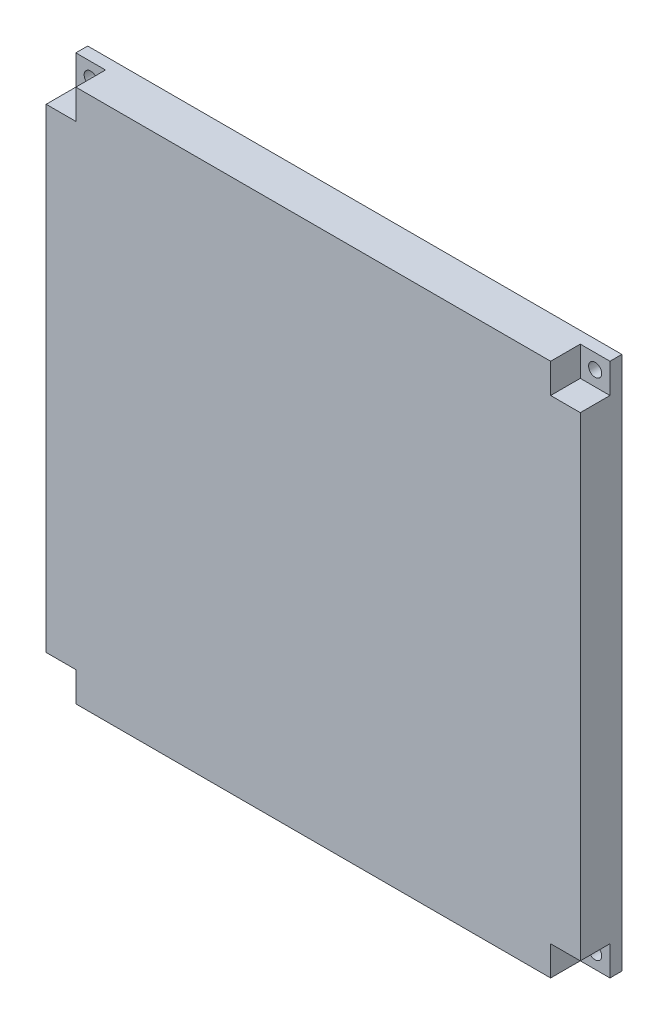
SolidWorks part; units mm, degrees
ref_plane "前基準面" through (0, 0, 0) normal (0, 0, 1) x (1, 0, 0)
ref_plane "上基準面" through (0, 0, 0) normal (0, 1, 0) x (1, 0, 0)
ref_plane "右基準面" through (0, 0, 0) normal (1, 0, 0) x (0, 0, -1)
sketch "草圖1" plane through (0, 0, 0) normal (0, 0, 1) x (1, 0, 0)
  line L1 (-89.0867, 42.9814) -> (10.9133, 42.9814)
  line L2 (-89.0867, 42.9814) -> (-89.0867, -47.0186)
  line L3 (-89.0867, -47.0186) -> (10.9133, -47.0186)
  line L4 (10.9133, 42.9814) -> (10.9133, -47.0186)
  dimension "D1" = 90
  dimension "D2" = 100
extrude "填料-伸長1" add sketch "草圖1" along normal blind 10 contours L4 L3 L2 L1
ref_plane "平面1" through (0, 0, 10) normal (0, 0, 1) x (1, 0, 0)
sketch "草圖6" plane through (0, 0, 10) normal (0, 0, 1) x (1, 0, 0)
  line L0 (-89.0867, -2.0186) -> (10.9133, -2.0186) construction
  line L1 (-89.0867, 42.9814) -> (-89.0867, -47.0186) construction
  line L2 (10.9133, 42.9814) -> (10.9133, -47.0186) construction
  line L3 (-39.0867, 42.9814) -> (-39.0867, -47.0186) construction
  line L4 (-89.0867, 42.9814) -> (10.9133, 42.9814) construction
  line L5 (-89.0867, -47.0186) -> (10.9133, -47.0186) construction
  line L6 (5.9133, 37.9814) -> (0.9133, 37.9814)
  line L7 (-84.0867, 42.9814) -> (-79.0867, 42.9814)
  line L8 (-84.0867, 42.9814) -> (-84.0867, 37.9814)
  line L9 (-84.0867, 37.9814) -> (-79.0867, 37.9814)
  line L10 (-79.0867, 42.9814) -> (-79.0867, 37.9814)
  line L11 (0.9133, 42.9814) -> (0.9133, 37.9814)
  line L12 (5.9133, 42.9814) -> (0.9133, 42.9814)
  line L13 (5.9133, 42.9814) -> (5.9133, 37.9814)
  line L14 (-84.0867, -42.0186) -> (-79.0867, -42.0186)
  line L15 (-79.0867, -47.0186) -> (-79.0867, -42.0186)
  line L16 (-84.0867, -47.0186) -> (-79.0867, -47.0186)
  line L17 (-84.0867, -47.0186) -> (-84.0867, -42.0186)
  line L18 (5.9133, -47.0186) -> (5.9133, -42.0186)
  line L19 (5.9133, -47.0186) -> (0.9133, -47.0186)
  line L20 (0.9133, -47.0186) -> (0.9133, -42.0186)
  line L21 (5.9133, -42.0186) -> (0.9133, -42.0186)
  dimension "D1" = 5
  dimension "D2" = 5
  dimension "D3" = 5
extrude "除料-伸長4" cut sketch "草圖6" against normal blind 5
ref_plane "平面2" through (0, 0, 0) normal (0, 0, -1) x (-1, 0, 0)
sketch "草圖7" plane through (0, 0, 0) normal (0, 0, -1) x (-1, 0, 0)
  line L0 (-10.9133, -2.0186) -> (89.0867, -2.0186) construction
  line L1 (-10.9133, 42.9814) -> (-10.9133, -47.0186) construction
  line L2 (89.0867, 42.9814) -> (89.0867, -47.0186) construction
  line L3 (39.0867, 42.9814) -> (39.0867, -47.0186) construction
  line L4 (89.0867, 42.9814) -> (-10.9133, 42.9814) construction
  line L5 (89.0867, -47.0186) -> (-10.9133, -47.0186) construction
  line L6 (84.0867, 37.9814) -> (79.0867, 37.9814)
  line L7 (-5.9133, 42.9814) -> (-0.9133, 42.9814)
  line L8 (-5.9133, 42.9814) -> (-5.9133, 37.9814)
  line L9 (-5.9133, 37.9814) -> (-0.9133, 37.9814)
  line L10 (-0.9133, 42.9814) -> (-0.9133, 37.9814)
  line L11 (79.0867, 42.9814) -> (79.0867, 37.9814)
  line L12 (84.0867, 42.9814) -> (79.0867, 42.9814)
  line L13 (84.0867, 42.9814) -> (84.0867, 37.9814)
  line L14 (84.0867, -47.0186) -> (84.0867, -42.0186)
  line L15 (84.0867, -47.0186) -> (79.0867, -47.0186)
  line L16 (79.0867, -47.0186) -> (79.0867, -42.0186)
  line L17 (84.0867, -42.0186) -> (79.0867, -42.0186)
  line L18 (-5.9133, -42.0186) -> (-0.9133, -42.0186)
  line L19 (-0.9133, -47.0186) -> (-0.9133, -42.0186)
  line L20 (-5.9133, -47.0186) -> (-0.9133, -47.0186)
  line L21 (-5.9133, -47.0186) -> (-5.9133, -42.0186)
  dimension "D1" = 5
  dimension "D2" = 5
  dimension "D3" = 5
extrude "除料-伸長5" cut sketch "草圖7" against normal blind 3
sketch "草圖8" plane through (0, 0, 0) normal (0, 0, -1) x (-1, 0, 0)
  line L0 (-10.9133, -2.0186) -> (89.0867, -2.0186) construction
  line L1 (-10.9133, 42.9814) -> (-10.9133, -47.0186) construction
  line L2 (89.0867, 42.9814) -> (89.0867, -47.0186) construction
  line L3 (39.0867, 42.9814) -> (39.0867, -47.0186) construction
  line L4 (79.0867, 42.9814) -> (-0.9133, 42.9814) construction
  line L5 (79.0867, -47.0186) -> (-0.9133, -47.0186) construction
  line L6 (-5.9133, 40.4814) -> (-0.9133, 40.4814) construction
  line L7 (-5.9133, 42.9814) -> (-5.9133, 37.9814) construction
  line L8 (-0.9133, 37.9814) -> (-0.9133, 42.9814) construction
  line L9 (-3.4133, 37.9814) -> (-3.4133, 42.9814) construction
  line L10 (-5.9133, 37.9814) -> (-0.9133, 37.9814) construction
  line L11 (-0.9133, 42.9814) -> (-5.9133, 42.9814) construction
  circle A0 centre (-3.4133, 40.4814) radius 1.1
  circle A1 centre (81.5867, 40.4814) radius 1.1
  circle A2 centre (81.5867, -44.5186) radius 1.1
  circle A3 centre (-3.4133, -44.5186) radius 1.1
  dimension "D1" = 2.2
extrude "除料-伸長6" cut sketch "草圖8" against normal blind 42
sketch "草圖10" plane through (0, 0, 0) normal (0, 0, 1) x (1, 0, 0)
  line L1 (-89.0867, 42.9814) -> (10.9133, 42.9814)
  line L2 (-89.0867, 42.9814) -> (-89.0867, -47.0186)
  line L3 (-89.0867, -47.0186) -> (10.9133, -47.0186)
  line L4 (10.9133, 42.9814) -> (10.9133, -47.0186)
extrude "除料-伸長7" cut sketch "草圖10" along normal blind 3
ref_plane "平面3" through (10.9133, 0, 0) normal (1, 0, 0) x (0, 0, -1)
sketch "草圖11" plane through (10.9133, 0, 0) normal (1, 0, 0) x (0, 0, -1)
  line L0 (-10, 44) -> (-10, -44) construction
  line L1 (-3, 42.9814) -> (-10, 42.9814)
  line L2 (-3, 42.9814) -> (-3, -47.0186)
  line L3 (-3, -47.0186) -> (-10, -47.0186)
  line L4 (-10, 42.9814) -> (-10, -47.0186)
  line L5 (-10, -47.0186) -> (-3, -47.0186) construction
extrude "除料-伸長8" cut sketch "草圖11" against normal blind 5
ref_plane "平面4" through (-89.0867, 0, 0) normal (-1, 0, 0) x (0, 0, 1)
sketch "草圖12" plane through (-89.0867, 0, 0) normal (-1, 0, 0) x (0, 0, 1)
  line L1 (3, 42.9814) -> (10, 42.9814)
  line L2 (3, 42.9814) -> (3, -47.0186)
  line L3 (3, -47.0186) -> (10, -47.0186)
  line L4 (10, 42.9814) -> (10, -47.0186)
extrude "除料-伸長9" cut sketch "草圖12" against normal blind 5
